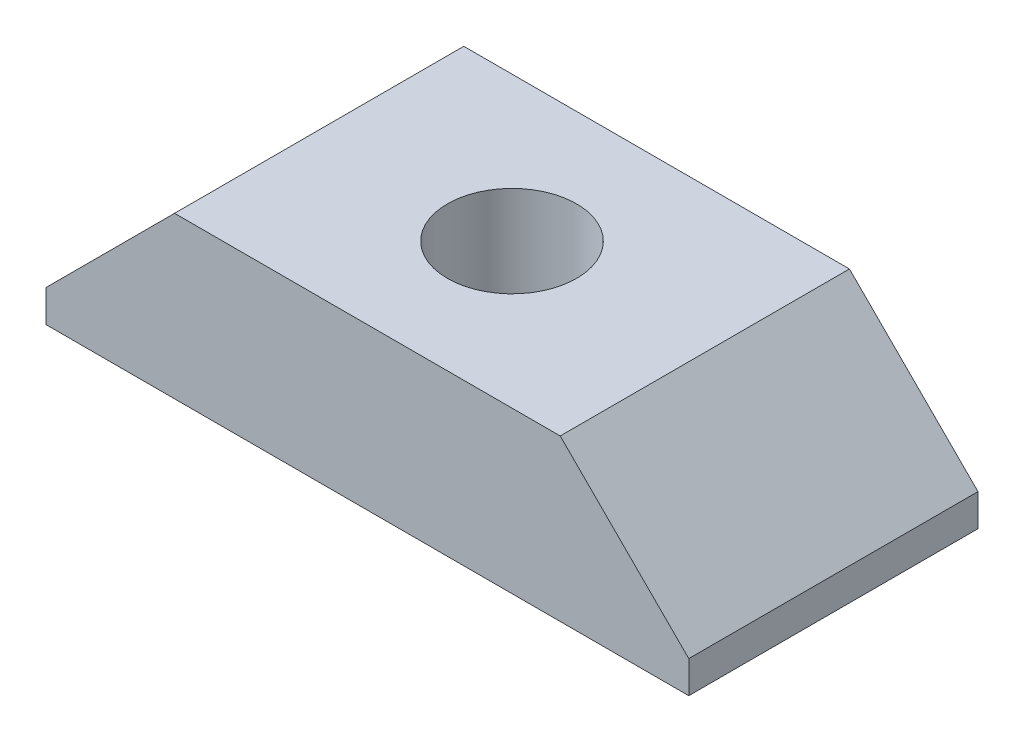
SolidWorks part; units mm, degrees
ref_plane "Front Plane" through (0, 0, 0) normal (0, 0, 1) x (1, 0, 0)
ref_plane "Top Plane" through (0, 0, 0) normal (0, 1, 0) x (1, 0, 0)
ref_plane "Right Plane" through (0, 0, 0) normal (1, 0, 0) x (0, 0, -1)
sketch "Sketch1" plane through (0, 0, 0) normal (0, 0, 1) x (1, 0, 0)
  line L1 (-12.7, -3.175) -> (12.7, -3.175)
  line L2 (-12.7, -3.175) -> (-12.7, 3.175)
  line L3 (-12.7, 3.175) -> (12.7, 3.175)
  line L4 (12.7, -3.175) -> (12.7, 3.175)
  line L5 (-12.7, -3.175) -> (12.7, 3.175) construction
  line L6 (-12.7, 3.175) -> (12.7, -3.175) construction
  point P0 (0, 0)
  dimension "D1" = 6.35
  dimension "D2" = 25.4
extrude "Boss-Extrude1" add sketch "Sketch1" along normal blind 11.43
chamfer "Chamfer2" distance 5.08 angle 45 2 edges at (12.7, 3.175, 5.715) (-12.7, 3.175, 5.715)
hole_wizard "1/4-20 Tapped Hole1" positions "Sketch3" profile "Sketch2" tap size "1/4-20" standard "Ansi Inch" end condition through all
sketch "Sketch3" plane through (0, 3.175, 0) normal (0, 1, 0) x (-1, 0, 0)
  line L0 (7.62, 0) -> (-7.62, 11.43) construction
  line L2 (7.62, 11.43) -> (-6.35, 0) construction
  line L3 (-7.62, 0) -> (7.62, 0) construction
  point P0 (0, 5.715)
cosmetic thread "Hole Thread1" parameters "D2"=6.35
sketch "Sketch2" plane through (0, 3.175, 5.715) normal (1, 0, 0) x (0, 0, 1)
  line L0 (0, 0) -> (0, 6.35)
  line L1 (0, 6.35) -> (2.5527, 6.35)
  line L2 (2.5527, 6.35) -> (2.5527, 0)
  line L5 (2.5527, 0) -> (0, 0)
  line L11 (0, -6.35) -> (0, 107.95) construction
  dimension "Thru Tap Drill Dia." = 5.1054
  dimension "Thru Tap Drill Depth" = 6.35
